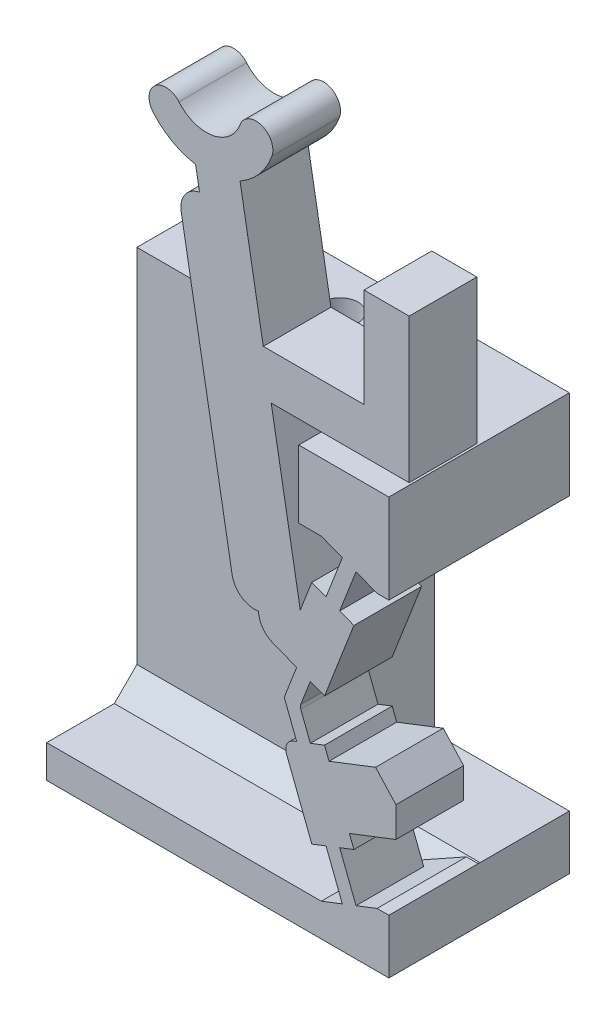
SolidWorks part; units mm, degrees
material "Nylon 6/12"
ref_plane "Front Plane" through (0, 0, 0) normal (0, 0, 1) x (1, 0, 0)
ref_plane "Top Plane" through (0, 0, 0) normal (0, 1, 0) x (1, 0, 0)
ref_plane "Right Plane" through (0, 0, 0) normal (1, 0, 0) x (0, 0, -1)
sketch "Sketch-SkeletonConfigUp" plane through (0, 0, 0) normal (0, 0, 1) x (1, 0, 0)
  line L0 (0, 0) -> (0, -50000) construction
  line L1 (-1.4217, 8.457) -> (-1.4217, 0) construction
  line L3 (0.7468, 14.0514) -> (-1.4217, 8.457) construction
  line L4 (-1.4217, 8.457) -> (0.7468, 2.8626) construction
  line L5 (0.7468, 14.0514) -> (2.1074, 19.3343) construction
  line L6 (-1.4217, 8.457) -> (-5.2203, 30) construction
  line L9 (0.7468, 14.0514) -> (0.7468, 2.8626) construction
  line L10 (0.7468, 2.8626) -> (0.7468, 0) construction
  line L11 (0, 0) -> (0.7468, 0) construction
  line L12 (0.7468, 0) -> (0, 0) construction
  dimension "D7" = 5.4552
  dimension "D10" = 6.745
  dimension "D3" = 2.1685
  dimension "D9" = 10
  dimension "D13" = 11.1888
  dimension "D14" = 30
  dimension "D5" = 10
  dimension "D2" = 21.8753
  dimension "D4" = 6
sketch "Sketch-SkeletonConfigDown" plane through (0, 0, 0) normal (0, 0, 1) x (1, 0, 0)
  line L0 (0, 0) -> (0, -50000) construction
  line L1 (0.7468, 14.0514) -> (0.7468, 2.8626) construction
  line L2 (5.9945, 14.5439) -> (0.7468, 14.0514) construction
  line L3 (0.7468, 14.0514) -> (2.9153, 8.457) construction
  line L4 (2.9153, 8.457) -> (0.7468, 2.8626) construction
  line L5 (0.7468, 14.0514) -> (-1.8086, 18.8711) construction
  line L6 (2.9153, 8.457) -> (-14.411, 21.8109) construction
  line L7 (0.7468, 2.8626) -> (5.9945, 14.5439) construction
  line L8 (-387.6937, -861.8102) -> (5.9945, 14.5439) construction
  line L10 (-1.4217, 8.457) -> (0.7468, 2.8626) construction
  line L11 (0.7468, 14.0514) -> (-1.4217, 8.457) construction
  line L12 (-1.4217, 8.457) -> (-5.2203, 30) construction
  line L13 (0.7468, 14.0514) -> (2.1074, 19.3343) construction
  dimension "D10" = 6.745
  dimension "D4" = 5.2707
  dimension "D5" = 119.553
  dimension "D2" = 52.378
  dimension "D3" = 31.19
ref_plane "Plane-Cam Base" through (3.8672, 0, 0) normal (1, 0, 0) x (0, 0, -1)
ref_plane "Plane-Down-to-Up Derailleur Clearance" through (1.3672, 0, 0) normal (1, 0, 0) x (0, 0, -1)
ref_plane "Plane-Cam Cavity Roof" through (-0.1328, 0, 0) normal (1, 0, 0) x (0, 0, -1)
sketch "Sketch-SwitchBossUp" plane through (0, 0, 0) normal (0, 0, 1) x (1, 0, 0)
  line L8 (-5.6979, 26.9497) -> (-5.5242, 25.9649)
  line L9 (-1.4217, 8.457) -> (-5.2203, 30) construction
  line L15 (-1.2188, 7.0342) -> (-0.6127, 7.2691) construction
  line L16 (-1.4217, 8.457) -> (0.7468, 2.8626) construction
  line L19 (0.0824, 13.2365) -> (0.6884, 13.0016) construction
  line L22 (0.8052, 15.1013) -> (1.4113, 14.8664) construction
  line L23 (-1.2188, 9.8799) -> (-1.8481, 10.1238)
  line L32 (1.0498, 2.9801) -> (0.4438, 2.7452) construction
  line L40 (-1.7703, 8.457) -> (-1.0732, 8.457) construction
  line L66 (-5.2203, 27.8193) -> (-5.2203, 50027.8193) construction
  line L74 (-4.078, 12.0039) -> (-6.3354, 24.8064)
  line L81 (2.3437, 2.4091) -> (2.8672, 2.4091)
  line L82 (-5.6111, 26.4573) -> (-3.6415, 26.8046) construction
  line L88 (-0.1116, 18.4627) -> (2.8672, 18.4627)
  line L92 (0.6672, 5.8348) -> (-1.1976, 5.1119) construction
  line L95 (-2.3469, 19.4627) -> (3.7672, 19.4627)
  line L96 (2.8672, 14.505) -> (2.8672, 18.4627)
  line L97 (3.7672, 19.4627) -> (3.7672, 25.8576)
  line L101 (-0.9157, 7.1517) -> (-1.4217, 8.457) construction
  line L103 (-5.2203, 30) -> (-3.0238, 29.2005) construction
  line L107 (-1.2188, 9.8799) -> (-0.6127, 9.6449) construction
  line L109 (-5.2203, 30) -> (-7.011, 28.4975) construction
  line L114 (0.0167, 7.5131) -> (-0.6127, 7.2691)
  line L117 (2.8672, 0) -> (-0.1272, 0)
  line L121 (0.7468, 0) -> (0, 0) construction
  line L122 (0.8052, 1.8128) -> (-0.1272, 1.4513)
  line L123 (1.4113, 2.0477) -> (2.3437, 2.4091)
  line L125 (2.8672, 2.4091) -> (2.8672, 0)
  line L127 (-0.6127, 9.6449) -> (0.0167, 9.401)
  line L133 (0.4438, 14.1689) -> (1.0498, 13.934) construction
  line L134 (0.0167, 9.401) -> (1.3178, 12.7576)
  line L135 (0.6884, 13.0016) -> (1.3178, 12.7576)
  line L142 (-0.1272, 1.4513) -> (-0.1272, 0)
  line L151 (0.0824, 13.2365) -> (-0.547, 13.4805)
  line L152 (0.8052, 15.1013) -> (0.0824, 13.2365)
  line L153 (1.4113, 14.8664) -> (0.6884, 13.0016)
  line L169 (0.0824, 3.6776) -> (0.8052, 1.8128)
  line L170 (1.4113, 2.0477) -> (0.6884, 3.9125)
  line L177 (0.6884, 3.9125) -> (0.0824, 3.6776) construction
  line L184 (-0.547, 13.4805) -> (-1.0591, 12.1594)
  line L191 (-1.2188, 7.0342) -> (-1.8481, 6.7902)
  line L197 (3.7672, 25.8576) -> (1.7672, 25.8576)
  line L205 (1.7672, 25.8576) -> (1.7672, 21.4627)
  line L207 (12.0045, 16.6962) -> (12.0045, 16.6883) construction
  line L218 (0.6884, 3.9125) -> (1.3178, 4.1564)
  line L225 (-1.0591, 12.1594) -> (-2.3469, 19.4627)
  line L235 (-5.5242, 25.9649) -> (-2.7958, 10.4912) construction
  line L236 (-1.8481, 6.7902) -> (-0.547, 3.4336)
  line L237 (-2.7958, 10.4912) -> (-2.9195, 11.1927)
  line L241 (-1.4217, 8.457) -> (-0.9157, 9.7624) construction
  line L242 (1.7672, 21.4627) -> (-2.6996, 21.4627)
  line L243 (-0.6127, 7.2691) -> (-1.0381, 8.3667)
  line L244 (-1.0381, 8.5474) -> (-0.6127, 9.6449)
  line L245 (-1.2188, 7.0342) -> (-1.7353, 8.3667)
  line L246 (-1.7353, 8.5474) -> (-1.2188, 9.8799)
  line L247 (0.0167, 7.5131) -> (0.2172, 6.9958)
  line L248 (0.8052, 1.8128) -> (1.4113, 2.0477) construction
  line L249 (0.0824, 3.6776) -> (-0.547, 3.4336)
  line L250 (-1.8481, 10.1238) -> (-0.547, 13.4805) construction
  line L251 (0.7468, 14.0514) -> (-1.4217, 8.457) construction
  line L252 (-1.2699, 11.6157) -> (0.5949, 10.8928) construction
  line L253 (-2.3469, 19.4627) -> (-2.6996, 21.4627) construction
  line L254 (-1.8481, 10.1238) -> (-2.7958, 10.4912)
  line L255 (0.8052, 15.1013) -> (-0.1272, 15.4627)
  line L256 (1.4113, 14.8664) -> (2.3437, 14.505)
  line L257 (2.3437, 14.505) -> (2.8672, 14.505)
  line L258 (-2.6996, 21.4627) -> (-3.7283, 27.297)
  line L259 (3.8672, -55) -> (3.8672, 55) construction
  line L260 (0.2172, 6.9958) -> (2.2792, 7.7951)
  line L261 (3.1794, 6.8085) -> (3.1794, 5.4731)
  line L262 (3.1794, 5.4731) -> (1.1173, 4.6738)
  line L263 (0.6672, 5.8348) -> (3.1794, 6.8085) construction
  line L264 (1.1173, 4.6738) -> (0.6672, 5.8348) construction
  line L265 (1.1173, 4.6738) -> (1.3178, 4.1564)
  line L266 (0.6672, 5.8348) -> (0.2172, 6.9958) construction
  line L267 (0.2172, 6.9958) -> (0.6672, 5.8348) construction
  line L268 (0.6672, 5.8348) -> (1.1173, 4.6738) construction
  line L269 (0.2172, 6.9958) -> (0.6672, 5.8348) construction
  line L270 (0.6672, 5.8348) -> (1.1173, 4.6738) construction
  line L271 (3.1794, 6.8085) -> (2.2792, 7.7951)
  line L272 (1.8311, 5.6598) -> (3.8672, 4.8706) construction
  line L273 (2.9153, 8.457) -> (0.7468, 2.8626) construction
  line L274 (-0.2652, 5.4733) -> (2.2792, 7.7951) construction
  line L275 (-0.2652, 5.4733) -> (3.8672, 5.4733) construction
  line L276 (-0.1272, 15.4627) -> (-1.1272, 15.4627)
  line L277 (-1.1272, 15.4627) -> (-1.1272, 18.4627)
  line L278 (-1.1272, 18.4627) -> (-0.1116, 18.4627)
  arc A0 (-3.7283, 27.297) -> (-2.319, 28.944) centre (-5.2203, 30) ccw
  arc A1 (-5.6979, 26.9497) -> (-7.5855, 28.0154) centre (-5.2203, 30) cw
  arc A2 (-7.5855, 28.0154) -> (-6.4364, 28.9796) centre (-7.011, 28.4975) cw
  arc A3 (-2.319, 28.944) -> (-3.7286, 29.457) centre (-3.0238, 29.2005) ccw
  arc A4 (-6.4364, 28.9796) -> (-3.7286, 29.457) centre (-5.2203, 30) ccw
  arc A19 (-6.3354, 24.8064) -> (-5.5242, 25.9649) centre (-5.3506, 24.98) cw
  circle A28 centre (-5.2203, 30) radius 2.3375 construction
  arc A30 (-4.078, 12.0039) -> (-2.9195, 11.1927) centre (-3.0932, 12.1775) ccw
  arc A31 (-1.0381, 8.3667) -> (-1.0381, 8.5474) centre (-0.805, 8.457) cw
  arc A32 (-1.7353, 8.3667) -> (-1.7353, 8.5474) centre (-1.5022, 8.457) cw
  point P5 (-4.6263, 26.6309)
  point P6 (-0.2652, 5.4733)
  point P45 (-0.3375, 11.2542)
  point P66 (4.5811, 6.2164)
  point P165 (0.7468, 14.0514)
  dimension "D23" = 1.5875
  dimension "D24" = 0.75
  dimension "D21" = 0.25
  dimension "D8" = 0.65
  dimension "D27" = 0.65
  dimension "D26" = 2
  dimension "D3" = 1.4
  dimension "D5" = 1.4
  dimension "D16" = 2
  dimension "D28" = 2
  dimension "D29" = 2
  dimension "D30" = 1
  dimension "D31" = 15
  dimension "D4" = 1.4169
  dimension "D6" = 0.65
  dimension "D7" = 2
  dimension "D11" = 1
  dimension "D10" = 1
  dimension "D9" = 0
  dimension "D12" = 60
  dimension "D13" = 60
  dimension "D14" = 2
  dimension "D15" = 1
  dimension "D17" = 2
  dimension "D19" = 0.1
  dimension "D22" = 42.38
  dimension "D18" = 3
  dimension "D25" = 1
  dimension "D32" = 1
  dimension "D20" = 1
extrude "Boss-Switch Body" add sketch "Sketch-SwitchBossUp" along normal blind 3
sketch "Sketch1" plane through (0, 0, 0) normal (0, 0, -1) x (-1, 0, 0)
  line L0 (-2.8672, 2.4091) -> (0.1272, 2.4091)
  line L1 (-2.8672, 0) -> (0.1272, 0)
  line L2 (-2.8672, 0) -> (-2.8672, 2.4091)
  line L4 (0.1272, 0) -> (0.1272, 2.4091)
  line L5 (1.1272, 14.505) -> (-2.8672, 14.505)
  line L10 (-2.8672, 14.505) -> (-2.8672, 18.4627)
  line L12 (-2.8672, 18.4627) -> (1.1272, 18.4627)
  line L14 (1.1272, 18.4627) -> (1.1272, 14.505)
  line L20 (-2.3437, 2.4091) -> (-2.8672, 2.4091) construction
  line L22 (-2.8672, 2.4091) -> (-2.3437, 2.4091) construction
  line L31 (0.1272, 0) -> (-2.8672, 0) construction
  line L32 (0.1272, 1.4513) -> (0.1272, 0) construction
extrude "Boss-Flange Width" add sketch "Sketch1" along normal blind 5
ref_plane "Plane-Sta2Sit Groove" through (-5.2203, 0, 0) normal (1, 0, 0) x (0, 0, -1)
ref_plane "Plane-Cam Outer Surface" through (-17.3003, 0, 0) normal (1, 0, 0) x (0, 0, -1)
ref_plane "Plane-FlangeTop" through (-12.3003, 0, 0) normal (1, 0, 0) x (0, 0, -1)
sketch "Sketch2" plane through (-12.3003, 0, 0) normal (1, 0, 0) x (0, 0, -1)
  line L0 (5, 18.4627) -> (-3, 18.4627) construction
  line L1 (5, 14.505) -> (1, 14.505)
  line L2 (5, 14.505) -> (5, 18.4627)
  line L3 (5, 18.4627) -> (1, 18.4627)
  line L4 (1, 14.505) -> (1, 18.4627)
  line L5 (5, 14.505) -> (-3, 14.505) construction
  line L11 (5, 1.4513) -> (-3, 1.4513)
  line L12 (5, 1.4513) -> (5, 0)
  line L13 (5, 0) -> (-3, 0)
  line L14 (-3, 1.4513) -> (-3, 0)
  line L15 (0, 8.457) -> (0, 30) construction
  line L16 (-3, 1.4513) -> (-3, 0) construction
  line L17 (5, 2.4091) -> (5, 0) construction
  line L19 (-3, 1.4513) -> (0, 1.4513) construction
  dimension "D1" = 1
extrude "Boss-Flange Height" add sketch "Sketch2" along normal up to surface (12.1731 mm away) up to face at (-0.1272, 1.2868, -0.6667)
sketch "Sketch17" plane through (0, 1.4513, 0) normal (0, -1, 0) x (1, 0, 0)
  line L0 (2.8672, -5) -> (-12.3003, -5)
  line L1 (2.8672, -5) -> (-12.3003, -5) construction
  line L2 (-12.3003, -5) -> (-12.3003, -1)
  line L3 (-12.3003, -1) -> (2.8672, -1)
  line L4 (2.8672, -1) -> (2.8672, -5)
  line L5 (-12.3003, -1) -> (-12.3003, -5) construction
  line L7 (-1.1272, -1) -> (-12.3003, -1) construction
extrude "Boss-Flange Support" add sketch "Sketch17" against normal up to surface (13.0536 mm away) up to face at (-1.4588, 14.505, -0.6)
sketch "Sketch27" plane through (0, 0, 0) normal (0, 0, 1) x (1, 0, 0)
  line L1 (-0.1272, 15.4627) -> (2.3437, 14.505)
  line L2 (2.3437, 14.505) -> (-1.1272, 14.505)
  line L3 (-1.1272, 14.505) -> (-1.1272, 15.4627)
  line L4 (-1.1272, 15.4627) -> (-0.1272, 15.4627)
  line L6 (-1.1272, 14.505) -> (2.8672, 14.505) construction
  line L7 (2.3437, 14.505) -> (1.2712, 14.505) construction
  line L8 (2.3437, 2.4091) -> (-0.1272, 2.4091)
  line L9 (-0.1272, 2.4091) -> (-0.1272, 1.4513)
  line L10 (-0.1272, 1.4513) -> (2.3437, 2.4091)
extrude "Cut-Wall Gap" cut sketch "Sketch27" against normal up to surface (1 mm away) up to face at (-2.6719, 9.207, -1)
ref_plane "Plane-Tap Depth" through (0, 13.4627, 0) normal (0, 1, 0) x (1, 0, 0)
sketch "Sketch-HolePositions" plane through (0, 0, 0) normal (0, -1, 0) x (1, 0, 0)
  line L0 (-12.3003, -3) -> (2.8672, -3) construction
  line L1 (2.8672, -5) -> (-12.3003, -5) construction
  line L2 (2.8672, -5) -> (2.8672, 3) construction
  line L4 (-12.3003, -22.2167) -> (-12.3003, 22.2167) construction
  point P6 (-9.3003, -3)
  point P7 (-5.3003, -3)
  dimension "D1" = 3
  dimension "D2" = 4
  dimension "D3" = 2
sketch "Sketch6" plane through (0, 0, 0) normal (0, -1, 0) x (-1, 0, 0)
  point P0 (9.3003, 3)
  point P3 (5.3003, 3)
hole_wizard "Tap Drill for M2x0.4 Tap1" positions "Sketch6" profile "Sketch5" hole size "M2x0.4" standard "ANSI Metric" end condition through all
sketch "Sketch5" plane through (-9.3003, 0, -3) normal (1, 0, 0) x (0, 0, -1)
  line L0 (0, 0) -> (0, 29.9505)
  line L1 (0, 29.9505) -> (0.8, 29.9505)
  line L2 (0.8, 29.9505) -> (0.8, 0)
  line L5 (0.8, 0) -> (0, 0)
  line L11 (0, -6.35) -> (0, 107.95) construction
  dimension "Thru Hole Dia." = 1.6
  dimension "Thru Hole Depth" = 29.9505
sketch "Sketch9" plane through (0, 0, 0) normal (0, -1, 0) x (1, 0, 0)
  point P0 (-9.3003, -3)
  point P3 (-5.3003, -3)
hole_wizard "M2 Clearance Hole2" positions "Sketch9" profile "Sketch8" hole size "M2" standard "ANSI Metric"
sketch "Sketch8" plane through (-9.3003, 0, -3) normal (1, 0, 0) x (0, 0, -1)
  line L0 (0, 0) -> (0, 14.1838)
  line L1 (0, 14.1838) -> (1.2, 13.4627)
  line L2 (1.2, 13.4627) -> (1.2, 0)
  line L5 (1.2, 0) -> (0, 0)
  line L10 (0, 14.1838) -> (-1.2, 13.4627) construction
  line L11 (0, -6.35) -> (0, 107.95) construction
  dimension "Hole Dia." = 2.4
  dimension "Hole Depth" = 13.4627
  dimension "Drill Angle" = 118
sketch "Sketch-Measurements for Derailleur Ramps" [suppressed] plane through (0, 0, 0) normal (0, 0, 1) x (1, 0, 0)
  line L0 (2.8784, 16.9852) -> (4.2265, 19.8331)
  line L1 (3.5524, 18.4092) -> (3.0492, 18.6474)
  line L2 (1.9779, 11.0613) -> (4.4465, 28.5428) construction
  line L3 (3.0492, 18.6474) -> (-4.0642, 13.8428)
  line L4 (7.1843, 11.0614) -> (-9.9544, 15.2993) construction
  line L5 (3.0492, 18.6474) -> (2.1536, 12.3053)
  line L6 (2.1536, 12.3053) -> (-4.0642, 13.8428)
  line L7 (-0.5075, 16.2451) -> (-0.5075, 18.6474)
  line L8 (-0.5075, 18.6474) -> (3.0492, 18.6474)
  line L9 (7.1843, 11.0614) -> (1.9779, 11.0613)
  line L10 (5.8827, 8.6389) -> (3.2795, 8.6389)
  line L12 (7.1843, 11.0614) -> (4.5811, 6.2164) construction
  line L13 (4.5811, 8.6389) -> (4.5811, 8.7912)
  line L14 (4.5811, 6.2164) -> (5.8827, 8.6389)
  line L15 (1.9779, 11.0613) -> (4.5811, 6.2164) construction
  line L16 (3.2795, 8.6389) -> (4.5811, 6.2164)
  line L17 (5.8827, 8.6389) -> (5.8827, 8.7912)
  dimension "D1" = 3.5567
  dimension "D2" = 1.3016
sketch "Sketch12" [suppressed] plane through (0, 23.1883, 0) normal (0, 1, 0) x (1, 0, 0)
  line L0 (10.0045, 0) -> (12.0045, -3)
  line L1 (12.0045, -3) -> (12.0045, 0)
  line L2 (12.0045, 0) -> (10.0045, 0)
extrude "Cut-Up-to-Down Cantilever Slope" [suppressed] cut sketch "Sketch12" against normal up to next
ref_plane "Plane1" [suppressed] through (0, 6.9404, 0) normal (0, 1, 0) x (1, 0, 0)
sketch "Sketch-Derailleur Location" [suppressed] plane through (0, 6.9404, 0) normal (0, 1, 0) x (1, 0, 0)
  line L0 (12.9465, 0) -> (12.9465, -3)
  line L1 (4.2399, -3) -> (3.2603, -3) construction
  line L2 (-119237.4187, 0) -> (9.8143, 0) construction
  point P0 (12.9465, 0)
  point P8 (12.9465, -1.5)
ref_plane "Plane-Cantilever Cut" [suppressed] through (7.0848, 8.5204, -1.9058) normal (-0.6301, -0.7578, 0.1695) x (-0.7765, 0.6151, -0.1368)
sketch "Sketch14" [suppressed] plane through (7.0848, 8.5204, -1.9058) normal (-0.6301, -0.7578, 0.1695) x (-0.7765, 0.6151, -0.1368)
  line L0 (2.3023, -1.6911) -> (-0.3551, -1.6911)
  line L2 (2.3023, -4.3362) -> (2.3023, -1.6911)
  line L3 (-0.3551, -1.6911) -> (-0.3551, -4.4608)
  line L5 (-0.3551, -4.4608) -> (1.0087, -5.0843)
  line L6 (1.0087, -5.0843) -> (2.3023, -4.3362)
extrude "Cut-Down-to-Up Cantilever Slope" [suppressed] cut sketch "Sketch14" against normal up to next
ref_plane "Plane-Symmetry Plane" through (0, 0, 1.5) normal (0, 0, 1) x (1, 0, 0)
sketch "Sketch-Cable Center Point" plane through (0, 0, 1.5) normal (0, 0, 1) x (1, 0, 0)
  line L0 (-5.2203, 30) -> (-5.0825, 29.2183)
  line L1 (-1.4217, 8.457) -> (-5.2203, 30) construction
  point P0 (-5.2203, 30)
  dimension "D1" = 0.7937
sketch "Sketch28" plane through (0, 0, -1) normal (0, 0, 1) x (1, 0, 0)
  line L0 (2.8672, 14.505) -> (2.8672, 2.4091)
  line L1 (2.3437, 2.4091) -> (2.8672, 2.4091) construction
  line L2 (2.8672, 14.505) -> (-3.1003, 14.505)
  line L3 (-3.1003, 14.505) -> (-3.1003, 2.4091)
  line L4 (-3.1003, 2.4091) -> (2.8672, 2.4091)
  line L6 (-6.5003, 13.4627) -> (-4.1003, 13.4627) construction
  line L7 (-6.5003, 13.4627) -> (-4.1003, 13.4627) construction
  dimension "D1" = 1
chamfer "Chamfer-Flange Support" [suppressed] distance 1.5 angle 45
chamfer "Chamfer-Flange Support 3" distance 1 angle 45 1 edges at (-6.2138, 1.4513, -1)
fillet "Fillet1" radius 1 1 edges at (-2.7958, 10.4912, 1.5)
fillet "Fillet2" radius 0.5 1 edges at (-1.8481, 6.7902, 1.5)
extrude "Cut-Print Support Clearance" cut sketch "Sketch28" against normal through all
equation "\"axle-diameter\"=2"
equation "\"switch-thickness\"=12"
equation "\"base-width\"=4.0"
equation "\"axle-bushing-radius\"=3"
equation "\"clearance\"= 0.25"
equation "\"arm-width\"=1.5"
equation "\"min-diameter\"=70"
equation "\"alpha\"=143.6120"
equation "\"gamma\"=119.5526"
equation "\"delta\"=145.9637"
equation "\"epsilon\"=6.7452"
equation "\"l_AB\"=8.8212"
equation "\"l_AC\"=4.4914"
equation "\"l_BD\"=5.2707"
equation "\"l_CD\"=3.8848"
equation "\"l_CE\"=10.9181"
equation "\"l_DF\"=5.4552"
equation "\"l_OA\"=7.7221"
equation "\"D7@Sketch-SkeletonConfigUp\" = \"l_DF\""
equation "\"D_groove\"=3.175"
equation "\"D5@Sketch-SkeletonConfigDown\" = \"gamma\""
equation "\"D4@Sketch-SkeletonConfigDown\" = \"l_BD\""
equation "\"hinge_length\"=1.5"
equation "\"hinge_depth\"=0.25"
equation "\"D10@Sketch-SkeletonConfigUp\"=\"epsilon\""
equation "\"D10@Sketch-SkeletonConfigDown\"=\"epsilon\""
equation "\"EE_dx\"=8.9056"
equation "\"EE_dy\"=8.1898"
equation "\"r_groove\"=\"D_groove\"/2"
equation "\"t_wall\"=25.4/16"
equation "\"width_lower\"=\"D_groove\"+\"t_wall\""
equation "\"cable_to_bottom\"=30.6257"
equation "\"switch_EE-up_base_dy\"=24"
equation "\"switch_EE-down_base_dy\"=16"
equation "\"D_axle\"=25.4/8"
equation "\"D_up_to_down\"=16"
equation "\"D_down_to_up\"=25"
equation "\"t_cam_base\"=7.5"
equation "\"D23@Sketch-SwitchBossUp\"=\"D_groove\"/2"
equation "\"D1@Sketch-Cable Center Point\"=\"D_groove\"/4"
